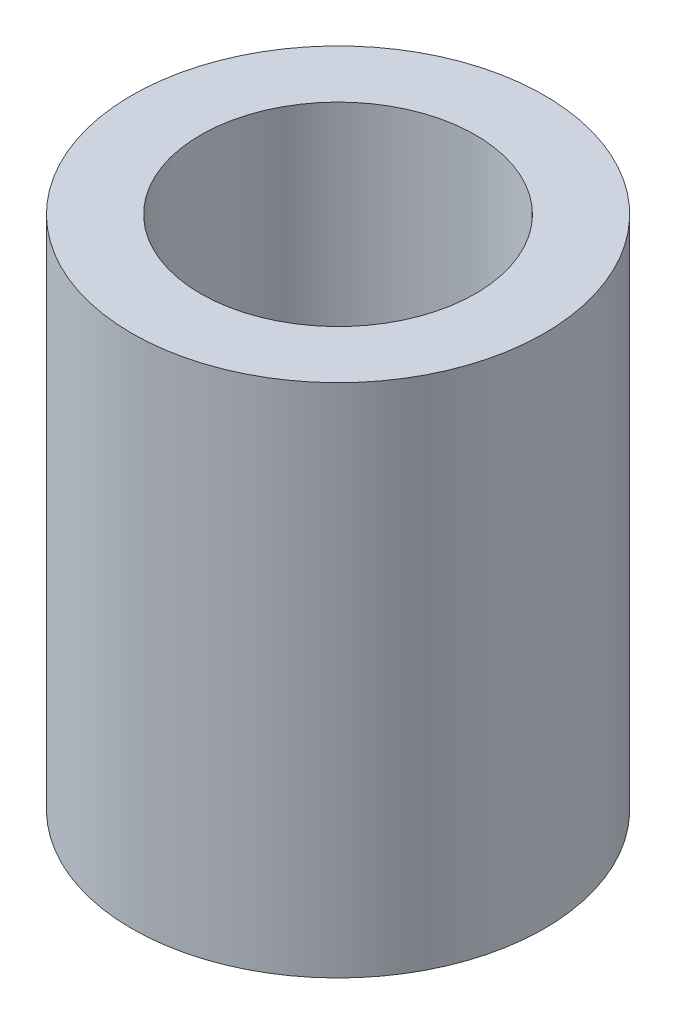
SolidWorks part; units mm, degrees
ref_plane "Front Plane" through (0, 0, 0) normal (0, 0, 1) x (1, 0, 0)
ref_plane "Top Plane" through (0, 0, 0) normal (0, 1, 0) x (1, 0, 0)
ref_plane "Right Plane" through (0, 0, 0) normal (1, 0, 0) x (0, 0, -1)
sketch "Sketch1" plane through (0, 0, 0) normal (0, 1, 0) x (1, 0, 0)
  circle A0 centre (0, 0) radius 6
extrude "Boss-Extrude1" add sketch "Sketch1" along normal blind 15
sketch "Sketch2" plane through (0, 0, 0) normal (0, -1, 0) x (1, 0, 0)
  circle A0 centre (0, 0) radius 3
extrude "Cut-Extrude1" cut sketch "Sketch2" against normal blind 7
sketch "Sketch3" plane through (0, 15, 0) normal (0, 1, 0) x (1, 0, 0)
  circle A0 centre (0, 0) radius 4
extrude "Cut-Extrude2" cut sketch "Sketch3" against normal blind 7
